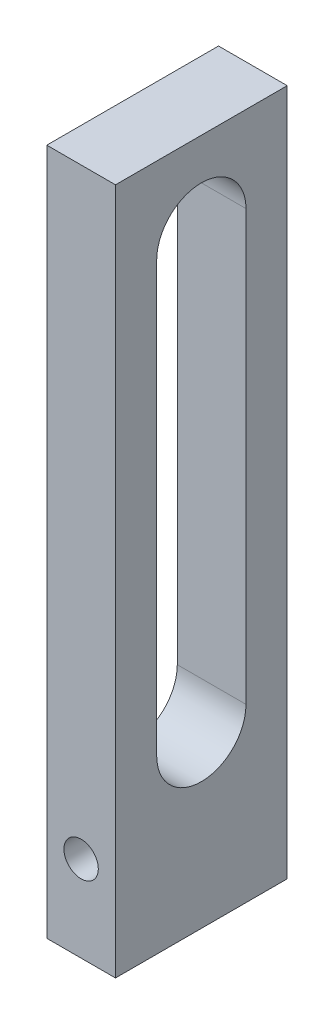
SolidWorks part; units mm, degrees
ref_plane "Front Plane" through (0, 0, 0) normal (0, 0, 1) x (1, 0, 0)
ref_plane "Top Plane" through (0, 0, 0) normal (0, 1, 0) x (1, 0, 0)
ref_plane "Right Plane" through (0, 0, 0) normal (1, 0, 0) x (0, 0, -1)
sketch "Sketch1" plane through (0, 0, 0) normal (0, 0, 1) x (1, 0, 0)
  line L1 (-4, -10) -> (4, -10)
  line L2 (-4, -10) -> (-4, 70)
  line L3 (-4, 70) -> (4, 70)
  line L4 (4, -10) -> (4, 70)
  circle A0 centre (0, 0) radius 2
  point P7 (0, -10)
  point P8 (0, -5.8262)
  point P9 (0, 0)
  point P10 (0, 0)
  dimension "D1" = 4
  dimension "D2" = 8
  dimension "D3" = 10
  dimension "D4" = 80
extrude "Main" add sketch "Sketch1" along normal mid plane 20
sketch "Sketch3" plane through (0, -10, 0) normal (0, -1, 0) x (-1, 0, 0)
  circle A0 centre (0, 0) radius 1.25
  dimension "D1" = 2.5
extrude "FixHole" cut sketch "Sketch3" against normal up to surface (8 mm away)
sketch "Sketch4" plane through (-4, 0, 0) normal (-1, 0, 0) x (0, 0, 1)
  line L0 (0, 10) -> (0, 60) construction
  line L1 (-5.2, 10) -> (-5.2, 60)
  line L2 (5.2, 10) -> (5.2, 60)
  line L3 (10, -10) -> (-10, -10) construction
  line L4 (10, 70) -> (-10, 70) construction
  line L5 (0, 51.108) -> (-80.8192, 110) construction
  line L6 (-80.8192, 110) -> (-80.8192, 10) construction
  arc A0 (-5.2, 10) -> (5.2, 10) centre (0, 10) ccw
  arc A1 (5.2, 60) -> (-5.2, 60) centre (0, 60) ccw
  circle A2 centre (0, 51.108) radius 5.2 construction
  point P3 (0, 35)
  point P14 (0, 19.0731)
  point P17 (0, 0)
  point P18 (0, 0)
  point P19 (-76.4675, 32.1839)
  point P20 (-84.3887, 89.8172)
  point P21 (-64.7224, 27.8136)
  point P22 (0, 0)
  point P23 (0, 0)
  point P24 (0, 0)
  point P25 (-63.6298, 26)
  point P26 (0, 38.4662)
  point P27 (-48.3338, 26)
  point P28 (0, 0)
  point P29 (0, 0)
  point P30 (-56.2549, 10)
  point P31 (72.1225, 10)
  point P32 (-71.5509, 10)
  point P33 (-88.4858, 10)
  point P34 (-80.8192, 10)
  dimension "D3" = 5.2
  dimension "D1" = 20
  dimension "D2" = 10
  dimension "D4" = 100
  dimension "D5" = 100
  dimension "D6" = 80.8192
extrude "RollingHole" cut sketch "Sketch4" against normal through all
